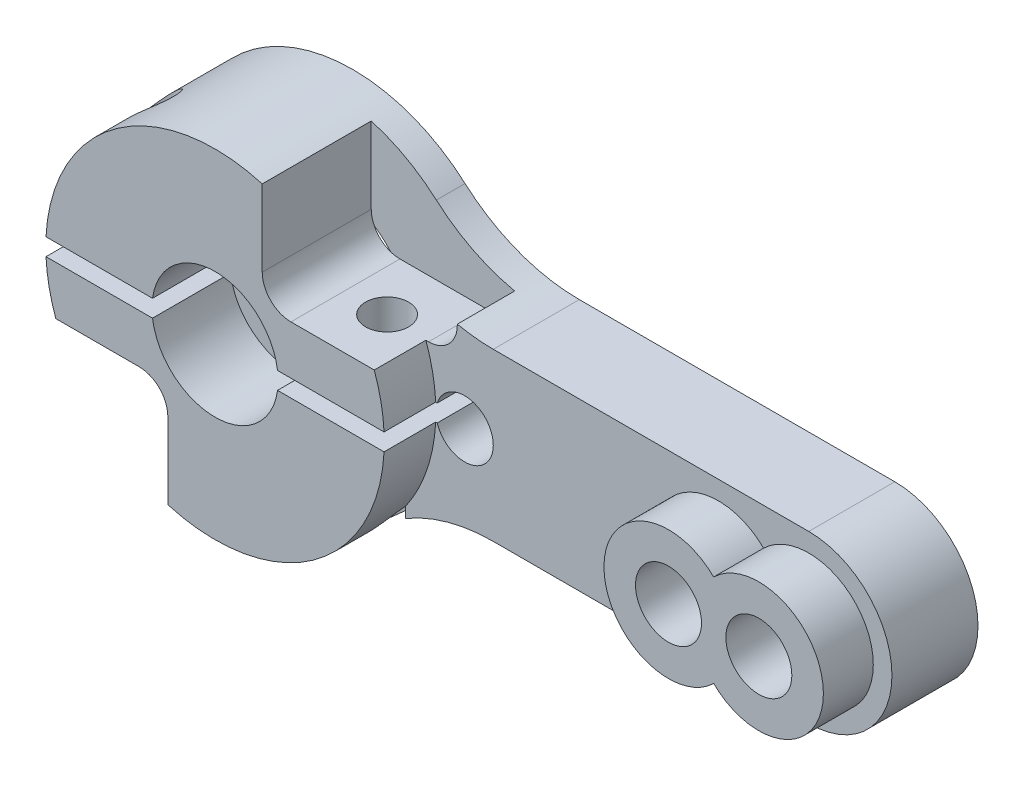
SolidWorks part; units mm, degrees
ref_plane "Front Plane" through (0, 0, 0) normal (0, 0, 1) x (1, 0, 0)
ref_plane "Top Plane" through (0, 0, 0) normal (0, 1, 0) x (1, 0, 0)
ref_plane "Right Plane" through (0, 0, 0) normal (1, 0, 0) x (0, 0, -1)
sketch "Sketch1" plane through (0, 0, 0) normal (0, 0, 1) x (1, 0, 0)
  line L0 (24, 3.683) -> (10.0322, 3.683)
  line L1 (24, -3.683) -> (10.0322, -3.683)
  arc A0 (4.9739, 5.604) -> (4.9739, -5.604) centre (0, 0) ccw
  arc A1 (24, -3.683) -> (24, 3.683) centre (24, 0) ccw
  arc A2 (4.9739, 5.604) -> (10.0322, 3.683) centre (10.0322, 11.303) ccw
  arc A3 (10.0322, -3.683) -> (4.9739, -5.604) centre (10.0322, -11.303) ccw
  circle A4 centre (24, 0) radius 1.4605
  circle A5 centre (20, 0) radius 1.4605
  circle A6 centre (0, 0) radius 1.524
  circle A7 centre (8.763, 0) radius 1.27
  dimension "D2" = 7.493
  dimension "D4" = 2.54
  dimension "D5" = 7.62
  dimension "D6" = 2.921
  dimension "D7" = 3.048
  dimension "D1" = 7.366
  dimension "D3" = 24
  dimension "D8" = 4
extrude "Boss-Extrude2" add sketch "Sketch1" along normal blind 3.81
sketch "Sketch2" plane through (0, 0, 3.81) normal (0, 0, 1) x (1, 0, 0)
  arc A0 (22, -2.0409) -> (22, 2.0409) centre (24, 0) ccw
  arc A1 (22, 2.0409) -> (22, -2.0409) centre (20, 0) ccw
  circle A2 centre (20, 0) radius 1.4605
  circle A3 centre (24, 0) radius 1.4605
  circle A4 centre (20, 0) radius 1.4605 construction
  dimension "D1" = 2.8575
extrude "Boss-Extrude3" add sketch "Sketch2" along normal blind 2.2098
sketch "Sketch3" plane through (0, 0, 3.81) normal (0, 0, 1) x (1, 0, 0)
  circle A0 centre (0, 0) radius 7.493
  arc A1 (4.9739, 5.604) -> (4.9739, -5.604) centre (0, 0) ccw construction
  circle A2 centre (0, 0) radius 2.794
  dimension "D1" = 5.588
extrude "Boss-Extrude4" add sketch "Sketch3" along normal blind 2.286
sketch "Sketch4" plane through (0, 0, 6.096) normal (0, 0, 1) x (1, 0, 0)
  circle A0 centre (0, 0) radius 2.794
  circle A1 centre (0, 0) radius 2.794 construction
extrude "Cut-Extrude1" cut sketch "Sketch4" against normal blind 3.4544
sketch "Sketch5" plane through (0, 0, 6.096) normal (0, 0, 1) x (1, 0, 0)
  line L0 (-2.0901, -8.6401) -> (-2.0901, -3.81)
  line L1 (-3.3601, -2.54) -> (-7.1701, -2.54)
  line L2 (-8.4401, -3.81) -> (-8.4401, -8.6401)
  line L3 (-8.4401, -8.6401) -> (-2.0901, -8.6401)
  line L4 (0, 0) -> (-14.2233, -16.1277) construction
  line L5 (-8.8999, 7.849) -> (11.6531, -10.277) construction
  line L6 (8.4401, 8.6401) -> (2.0901, 8.6401)
  line L7 (8.4401, 3.81) -> (8.4401, 8.6401)
  line L8 (3.3601, 2.54) -> (7.1701, 2.54)
  line L9 (2.0901, 8.6401) -> (2.0901, 3.81)
  arc A0 (-3.3601, -2.54) -> (-2.0901, -3.81) centre (-3.3601, -3.81) cw
  arc A1 (-8.4401, -3.81) -> (-7.1701, -2.54) centre (-7.1701, -3.81) cw
  arc A2 (8.4401, 3.81) -> (7.1701, 2.54) centre (7.1701, 3.81) cw
  arc A3 (3.3601, 2.54) -> (2.0901, 3.81) centre (3.3601, 3.81) cw
  point P24 (0, 0)
  dimension "D1" = 6.35
  dimension "D3" = 1.27
  dimension "D6" = 1.27
  dimension "D2" = 5.08
  dimension "D4" = 90
  dimension "D5" = 2.54
  dimension "D7" = 2
extrude "Cut-Extrude2" cut sketch "Sketch5" against normal blind 4.826
sketch "Sketch6" plane through (0, -2.54, 0) normal (0, -1, 0) x (-1, 0, 0)
  line L1 (7.0494, -1.27) -> (7.0494, -6.096) construction
  line L2 (3.3601, -6.096) -> (7.0494, -6.096) construction
  circle A0 centre (5.2047, -3.683) radius 0.9525
  point P6 (7.0494, -3.683)
  point P8 (5.2047, -6.096)
  dimension "D1" = 1.905
extrude "Cut-Extrude3" cut sketch "Sketch6" against normal through all
sketch "Sketch7" plane through (0, 2.54, 0) normal (0, 1, 0) x (1, 0, 0)
  line L0 (3.3601, -1.27) -> (3.3601, -6.096) construction
  line L1 (3.3601, -6.096) -> (7.0494, -6.096) construction
  circle A0 centre (5.2047, -3.683) radius 0.9525
  point P5 (3.3601, -3.683)
  point P8 (5.2047, -6.096)
  dimension "D1" = 1.905
extrude "Cut-Extrude4" cut sketch "Sketch7" against normal through all
sketch "Sketch8" plane through (0, 0, 6.096) normal (0, 0, 1) x (1, 0, 0)
  line L1 (8.4077, 0.381) -> (-7.493, 0.381)
  line L2 (8.4077, 0.381) -> (8.4077, -0.381)
  line L3 (8.4077, -0.381) -> (-7.493, -0.381)
  line L4 (-7.493, 0.381) -> (-7.493, -0.381)
  arc A0 (2.0901, 7.1956) -> (-7.0494, -2.54) centre (0, 0) ccw construction
  point P7 (8.4077, 0)
  dimension "D1" = 0.762
  dimension "D2" = 8.4077
extrude "Cut-Extrude5" cut sketch "Sketch8" against normal through all
sketch "Sketch9" plane through (0, 0, 0) normal (0, 0, -1) x (-1, 0, 0)
  circle A0 centre (0, 0) radius 3.937
  dimension "D1" = 7.874
extrude "Cut-Extrude6" cut sketch "Sketch9" against normal blind 1.27
